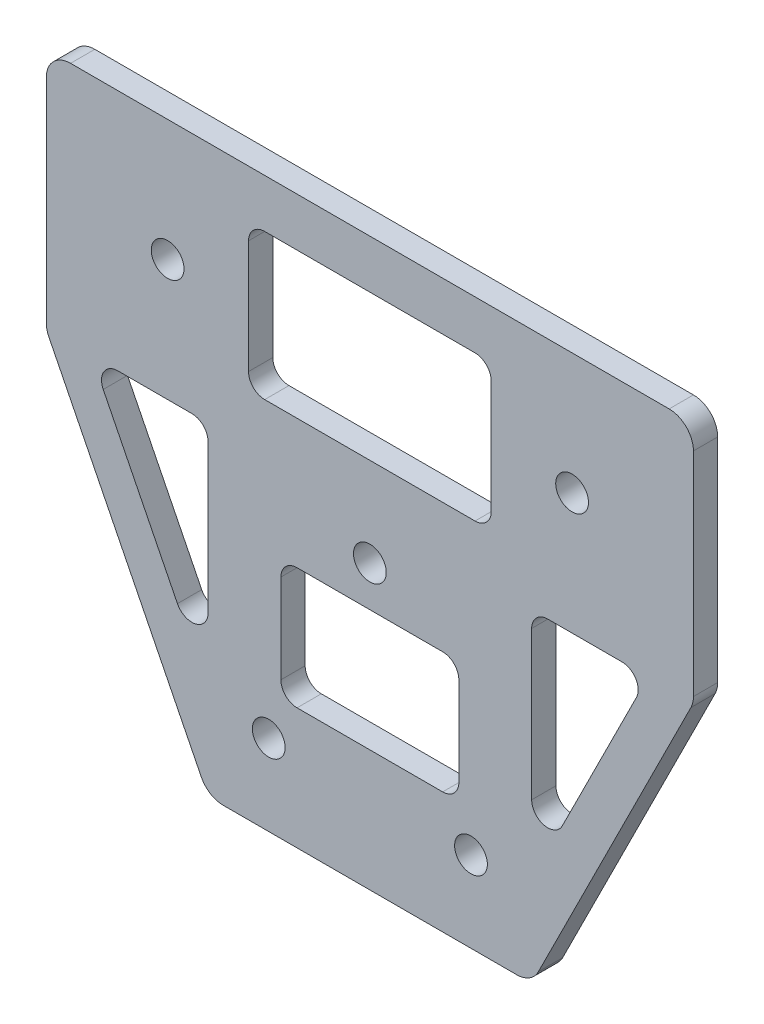
SolidWorks part; units mm, degrees
material "Thornel Mat VMA"
ref_plane "前视基准面" through (0, 0, 0) normal (0, 0, 1) x (1, 0, 0)
ref_plane "上视基准面" through (0, 0, 0) normal (0, 1, 0) x (1, 0, 0)
ref_plane "右视基准面" through (0, 0, 0) normal (1, 0, 0) x (0, 0, -1)
other "Configuration Table"
sketch "草图1" plane through (0, 0, 0) normal (0, 0, 1) x (1, 0, 0)
  line L0 (-40, 0) -> (40, 0)
  line L1 (40, 0) -> (40, -30)
  line L2 (40, -30) -> (20, -70)
  line L3 (20, -70) -> (-20, -70)
  line L4 (-20, -70) -> (-40, -30)
  line L5 (-40, -30) -> (-40, 0)
  point P5 (0, -70)
  dimension "D1" = 40
  dimension "D2" = 80
  dimension "D3" = 70
  dimension "D4" = 30
extrude "凸台-拉伸1" add sketch "草图1" along normal blind 3
sketch "草图2" plane through (0, 0, 3) normal (0, 0, 1) x (1, 0, 0)
  line L0 (40, 0) -> (-40, 0) construction
  line L1 (-20, -70) -> (20, -70) construction
  line L2 (0, 0) -> (0, -35) construction
  line L3 (-20, -70) -> (20, -70) construction
  line L4 (0, -60) -> (0, -70) construction
  circle A0 centre (-25, -15) radius 2.025
  circle A1 centre (25, -15) radius 2.025
  circle A2 centre (0, -35) radius 2.025
  circle A3 centre (0, -60) radius 2.025 construction
  circle A4 centre (12.5, -60) radius 2.025
  circle A5 centre (-12.5, -60) radius 2.025
  point P20 (0, -70)
  dimension "D1" = 4.05
  dimension "D3" = 10
  dimension "D4" = 25
  dimension "D5" = 50
  dimension "D6" = 4.05
  dimension "D9" = 25
  dimension "D2" = 15
  dimension "D7" = 10
extrude "切除-拉伸1" cut sketch "草图2" against normal blind 3
sketch "草图3" plane through (0, 0, 3) normal (0, 0, 1) x (1, 0, 0)
  line L0 (-34.4098, -30) -> (-20, -30)
  line L1 (-15, -24) -> (15, -24)
  line L2 (-15, -24) -> (-15, -6)
  line L3 (-15, -6) -> (15, -6)
  line L4 (15, -24) -> (15, -6)
  line L5 (-15, -24) -> (15, -6) construction
  line L6 (-15, -6) -> (15, -24) construction
  line L7 (-11, -55) -> (11, -55)
  line L8 (-11, -55) -> (-11, -40)
  line L9 (-11, -40) -> (11, -40)
  line L10 (11, -55) -> (11, -40)
  line L11 (-11, -55) -> (11, -40) construction
  line L12 (-11, -40) -> (11, -55) construction
  line L13 (-20, -30) -> (-20, -58.8197)
  line L14 (-20, -58.8197) -> (-34.4098, -30)
  line L15 (20, -30) -> (20, -58.8197)
  line L16 (20, -58.8197) -> (34.4098, -30)
  line L17 (34.4098, -30) -> (20, -30)
  line L18 (20, -70) -> (40, -30) construction
  line L19 (-40, -30) -> (-20, -70) construction
  line L20 (0, -35) -> (0, -60) construction
  line L21 (25, -15) -> (-25, -15) construction
  point P0 (0, -15)
  point P5 (0, -47.5)
  point P16 (0, 0)
  dimension "D1" = 5
  dimension "D2" = 5
  dimension "D3" = 40
  dimension "D4" = 25
  dimension "D5" = 22
  dimension "D6" = 15
  dimension "D7" = 18
  dimension "D8" = 30
extrude "切除-拉伸2" cut sketch "草图3" against normal blind 3 contours L1 L4 L3 L2 | L14 L13 L0 | L20 L9 L8 L7 | L9 L20 L7 L10 | L16 L17 L15
fillet "圆角1" radius 2 14 edges at (-20, -58.8197, 1.5) (-34.4098, -30, 1.5) (20, -58.8197, 1.5) (20, -30, 1.5) (34.4098, -30, 1.5) (-11, -55, 1.5) (-11, -40, 1.5) (11, -40, 1.5) (11, -55, 1.5) (-15, -24, 1.5) (-15, -6, 1.5) (15, -6, 1.5) (15, -24, 1.5) (-20, -30, 1.5)
fillet "圆角2" radius 3 6 edges at (40, 0, 1.5) (40, -30, 1.5) (20, -70, 1.5) (-20, -70, 1.5) (-40, -30, 1.5) (-40, 0, 1.5)
